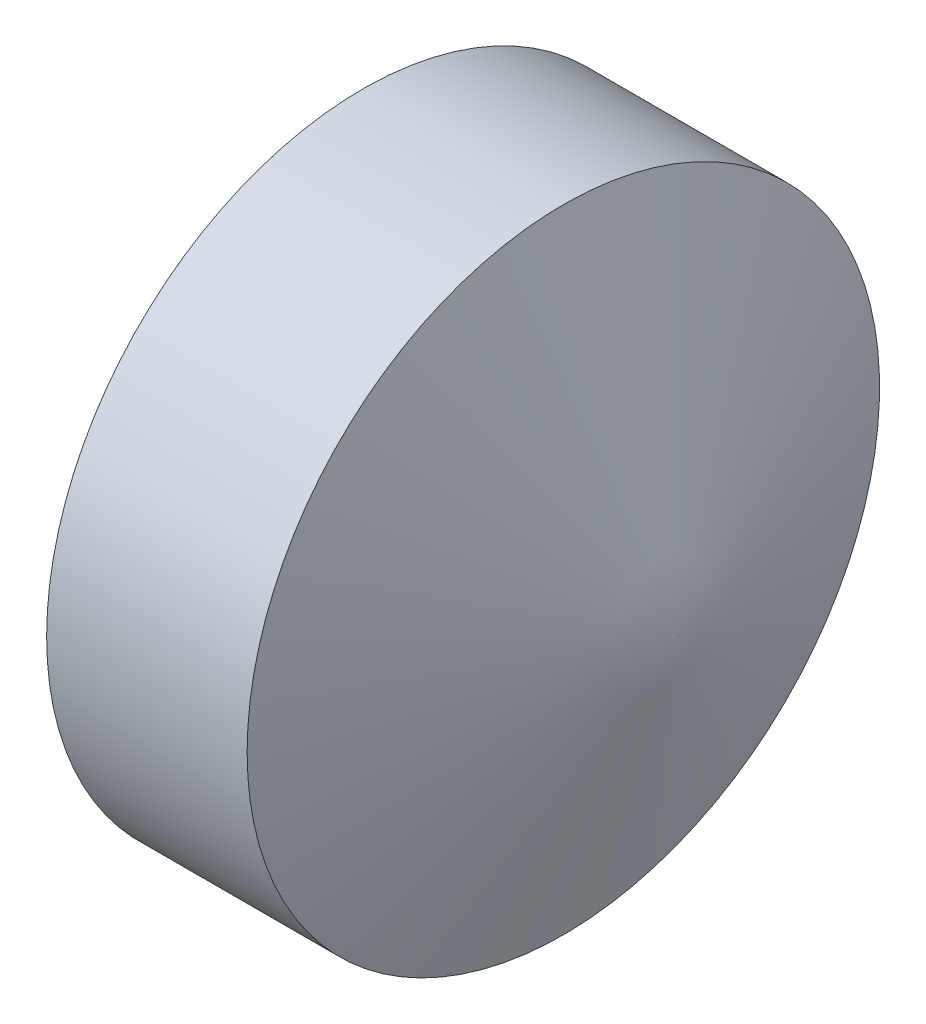
SolidWorks part; units mm, degrees
material "AISI 4340 Aço recozido"
ref_plane "Plano frontal" through (0, 0, 0) normal (0, 0, 1) x (1, 0, 0)
ref_plane "Plano superior" through (0, 0, 0) normal (0, 1, 0) x (1, 0, 0)
ref_plane "Plano direito" through (0, 0, 0) normal (1, 0, 0) x (0, 0, -1)
ref_plane "Plano1" through (0, 0, 0) normal (0, 0, -1) x (-1, 0, 0)
sketch "Esboço1" plane through (0, 0, 0) normal (0, 0, -1) x (-1, 0, 0)
  line L0 (-2.5063, 1.3563) -> (-3, 0)
  line L1 (-3, 0) -> (-1.5, 0)
  line L2 (-1.5, 0) -> (-1.5, 1.3563)
  line L3 (-1.5, 1.3563) -> (-2.5063, 1.3563)
  line L4 (-3, 0) -> (-1.5, 0) construction
  dimension "D1" = 70
  dimension "D2" = 1.5
revolve "Revolução1" add sketch "Esboço1" angle 360 about L4
sketch "Esboço2" plane through (1.5, 0, 0) normal (-1, 0, 0) x (0, 0, 1)
  line L0 (0.3753, -0.65) -> (0.7506, 0)
  line L1 (0.7506, 0) -> (0.3753, 0.65)
  line L2 (0.3753, 0.65) -> (-0.3753, 0.65)
  line L3 (-0.3753, 0.65) -> (-0.7506, 0)
  line L4 (-0.7506, 0) -> (-0.3753, -0.65)
  line L5 (-0.3753, -0.65) -> (0.3753, -0.65)
extrude "Corte-extrusão1" cut sketch "Esboço2" against normal blind 1.2
chamfer "Chanfro1" distance 0.2535 angle 30 1 edges at (1.5, 0, 1.3563)
